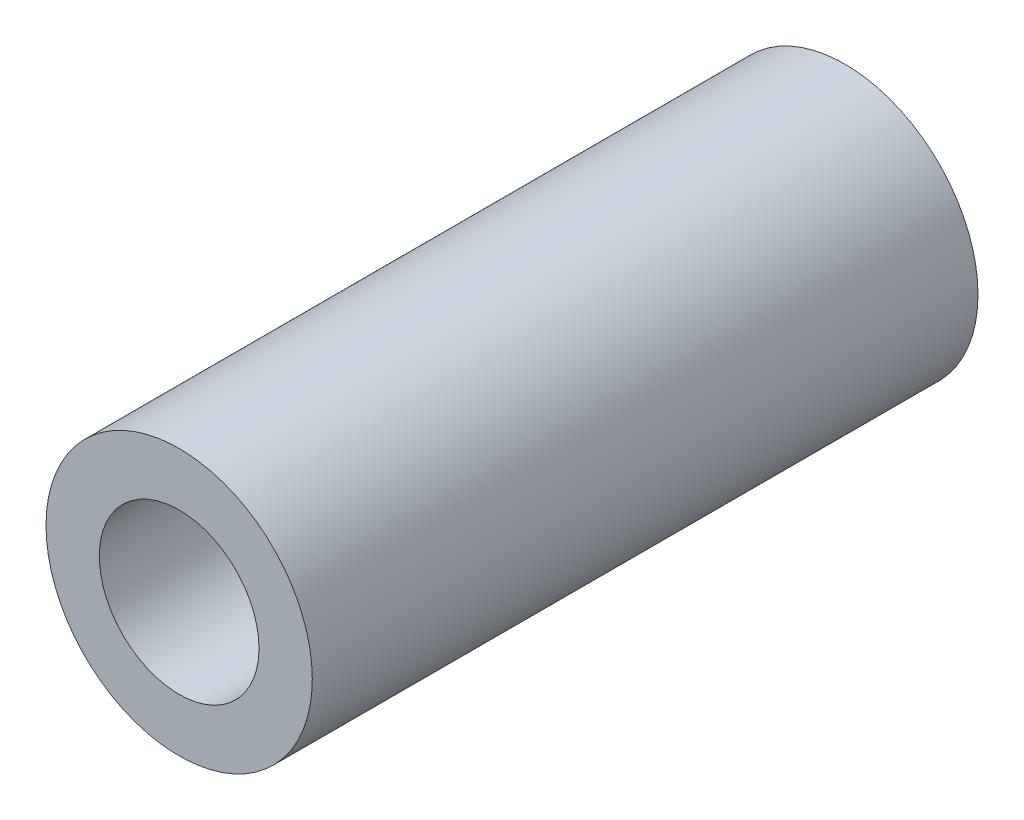
SolidWorks part; units mm, degrees
material "Delrin 2700 NC010, Low Viscosity Acetal Copolymer (SS)"
ref_plane "Front Plane" through (0, 0, 0) normal (0, 0, 1) x (1, 0, 0)
ref_plane "Top Plane" through (0, 0, 0) normal (0, 1, 0) x (1, 0, 0)
ref_plane "Right Plane" through (0, 0, 0) normal (1, 0, 0) x (0, 0, -1)
sketch "Sketch1" plane through (0, 0, 0) normal (0, 0, 1) x (1, 0, 0)
  circle A0 centre (0, 0) radius 3
  circle A1 centre (0, 0) radius 5
  dimension "D1" = 6
  dimension "D2" = 2
extrude "Boss-Extrude1" add sketch "Sketch1" along normal blind 25
